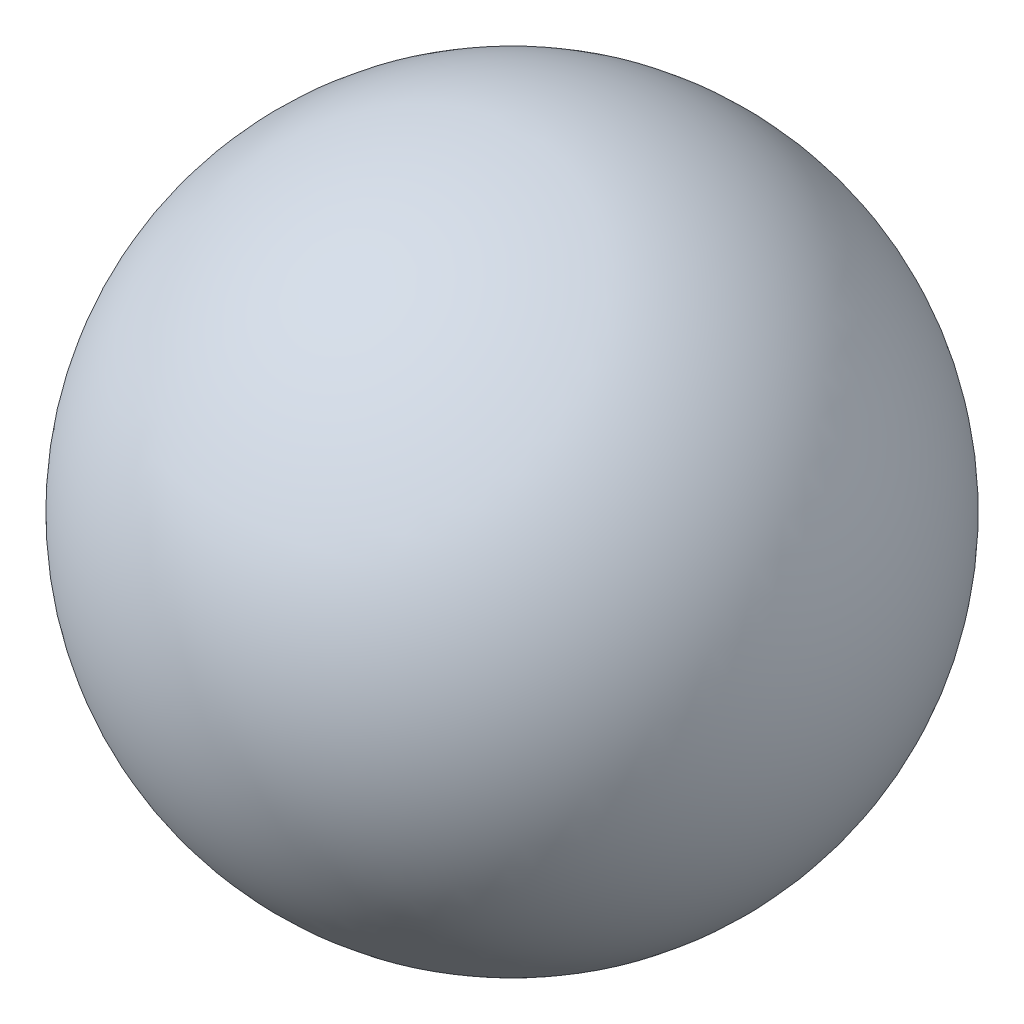
SolidWorks part; units mm, degrees
ref_plane "Alzado" through (0, 0, 0) normal (0, 0, 1) x (1, 0, 0)
ref_plane "Planta" through (0, 0, 0) normal (0, 1, 0) x (1, 0, 0)
ref_plane "Vista lateral" through (0, 0, 0) normal (1, 0, 0) x (0, 0, -1)
sketch "Croquis1" plane through (0, 0, 0) normal (0, 0, 1) x (1, 0, 0)
  line L0 (0, 15) -> (0, -49985) construction
  circle A0 centre (0, 0) radius 15
  dimension "D1" = 30
revolve "Revolución2" add sketch "Croquis1" angle 360 about L0
